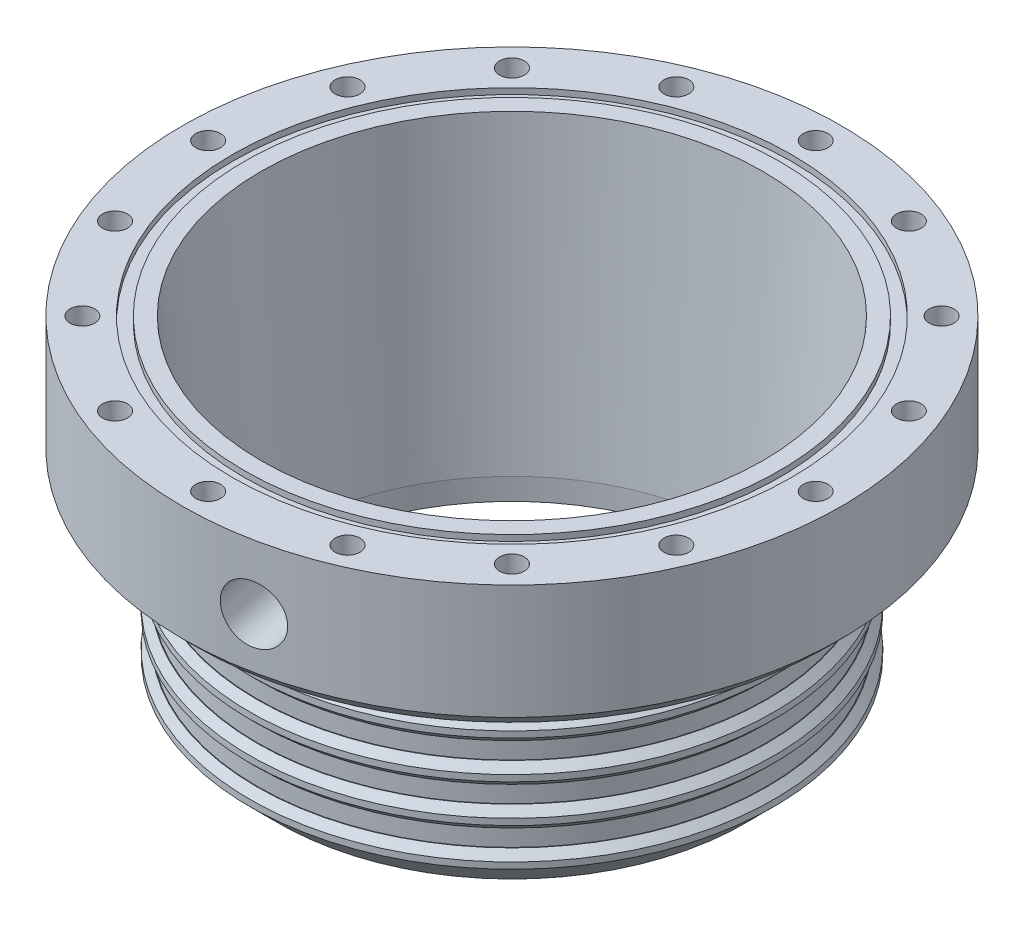
SolidWorks part; units mm, degrees
material "6061-T4 (SS)"
ref_plane "Front Plane" through (0, 0, 0) normal (0, 0, 1) x (1, 0, 0)
ref_plane "Top Plane" through (0, 0, 0) normal (0, 1, 0) x (1, 0, 0)
ref_plane "Right Plane" through (0, 0, 0) normal (1, 0, 0) x (0, 0, -1)
sketch "Sketch1" plane through (0, 0, 0) normal (0, 1, 0) x (1, 0, 0)
  circle A0 centre (0, 0) radius 55.5625
  circle A1 centre (0, 0) radius 58.1025
  dimension "D1" = 111.125
  dimension "D2" = 2.54
extrude "Boss-Extrude1" add sketch "Sketch1" along normal blind 38.1
sketch "Sketch2" plane through (0, 38.1, 0) normal (0, 1, 0) x (1, 0, 0)
  circle A0 centre (0, 0) radius 55.5625
  circle A1 centre (0, 0) radius 73.025
  circle A2 centre (0, 0) radius 55.5625 construction
  dimension "D1" = 146.05
extrude "Boss-Extrude2" add sketch "Sketch2" along normal blind 28.575
sketch "Sketch7" plane through (0, 0, 0) normal (0, 0, 1) x (1, 0, 0)
  line L0 (0, 0) -> (0, 88.9) construction
ref_plane "Plane1" through (0, 0, 0) normal (0.9659, 0, -0.2588) x (0, 1, 0)
ref_plane "Plane2" through (18.9003, 0, 70.5367) normal (0.2588, 0, 0.9659) x (0.9659, 0, -0.2588)
sketch "Sketch9" plane through (0, 0, 0) normal (0, 0, 1) x (1, 0, 0)
  line L0 (0, 0) -> (0, 88.9) construction
  line L2 (0, 0) -> (-58.1025, 0) construction
  line L3 (-58.1025, 0) -> (58.1025, 0) construction
  line L4 (-58.1025, 0) -> (-58.1025, 38.1) construction
  line L5 (-73.025, 38.1) -> (73.025, 38.1) construction
  line L6 (-58.1025, 38.1) -> (58.1025, 38.1) construction
  line L7 (-58.1025, 38.1) -> (-58.1025, 33.528)
  line L8 (-58.1025, 4.572) -> (-56.388, 4.572)
  line L9 (-58.1025, 4.572) -> (-58.1025, 8.382)
  line L10 (-58.1025, 8.382) -> (-56.388, 8.382)
  line L11 (-56.388, 4.572) -> (-56.388, 8.382)
  line L12 (-58.1025, 12.954) -> (-56.388, 12.954)
  line L13 (-58.1025, 12.954) -> (-58.1025, 16.764)
  line L14 (-58.1025, 16.764) -> (-56.388, 16.764)
  line L15 (-56.388, 12.954) -> (-56.388, 16.764)
  line L16 (-58.1025, 21.336) -> (-56.388, 21.336)
  line L17 (-58.1025, 21.336) -> (-58.1025, 25.146)
  line L18 (-58.1025, 25.146) -> (-56.388, 25.146)
  line L19 (-56.388, 21.336) -> (-56.388, 25.146)
  line L20 (-58.1025, 29.718) -> (-56.388, 29.718)
  line L21 (-58.1025, 29.718) -> (-58.1025, 33.528)
  line L22 (-58.1025, 33.528) -> (-56.388, 33.528)
  line L23 (-56.388, 29.718) -> (-56.388, 33.528)
  line L24 (-58.1025, 29.718) -> (-58.1025, 25.146)
  line L25 (-58.1025, 21.336) -> (-58.1025, 16.764)
  line L26 (-58.1025, 12.954) -> (-58.1025, 8.382)
  line L27 (-58.1025, 4.572) -> (-58.1025, 0)
  dimension "D1" = 58.1025
  dimension "D2" = 1.7145
  dimension "D3" = 3.81
revolve "Cut-Revolve1" cut sketch "Sketch9" angle 360 about L0
chamfer "Chamfer1" distance 1.5875 angle 45 1 edges at (0, 0, 58.1025)
sketch "Sketch10" plane through (0, 0, 0) normal (0, 0, 1) x (1, 0, 0)
  line L0 (0, 0) -> (0, 88.7441) construction
  line L1 (0, 0) -> (55.5625, 0) construction
  line L2 (55.5625, 0) -> (55.5625, 66.675)
  line L3 (55.5625, 66.675) -> (50.8, 0)
  line L4 (50.8, 0) -> (55.5625, 0)
  dimension "D1" = 55.5625
  dimension "D2" = 66.675
  dimension "D3" = 50.8
revolve "Revolve1" add sketch "Sketch10" angle 360 about L0
sketch "Sketch11" plane through (0, 66.675, 0) normal (0, 1, 0) x (1, 0, 0)
  circle A0 centre (0, 0) radius 61.9633
  circle A1 centre (0, 0) radius 59.3217
  dimension "D1" = 123.9266
  dimension "D2" = 2.6416
extrude "Cut-Extrude5" cut sketch "Sketch11" against normal blind 1.3208
sketch "Sketch12" plane through (0, 66.675, 0) normal (0, 1, 0) x (1, 0, 0)
  circle A0 centre (0, 0) radius 67.31 construction
  circle A1 centre (0, -67.31) radius 2.7432
  dimension "D1" = 5.4864
  dimension "D2" = 134.62
extrude "Cut-Extrude7" cut sketch "Sketch12" against normal blind 20.955 contours A1
pattern_circular "CirPattern2" count 16 over 360 about axis through (0, 0, 0) along (0, 1, 0) of "Cut-Extrude7"
sketch "Sketch13" plane through (0, 0, 0) normal (0, 0, 1) x (1, 0, 0)
  line L0 (0, 0) -> (50.8, 0) construction
  line L1 (0, 0) -> (0, 34.9502) construction
  line L2 (50.8, 0) -> (56.515, 0)
  line L3 (50.8, 0) -> (50.8, -5.715)
  line L4 (56.515, 0) -> (50.8, -5.715)
  dimension "D1" = 50.8
  dimension "D2" = 5.715
  dimension "D3" = 45
revolve "Revolve2" add sketch "Sketch13" angle 360 about L1
chamfer "Chamfer2" distance 1.27 angle 45 1 edges at (0, -5.715, -50.8)
sketch "Sketch14" plane through (0, 66.675, 0) normal (0, 1, 0) x (1, 0, 0)
  line L0 (0, -67.31) -> (25.7584, -62.1863) construction
  line L1 (0, -36.6713) -> (0, 36.6713) construction
  line L2 (0, 0) -> (12.8792, -64.7482) construction
  circle A1 centre (0, -67.31) radius 2.7432 construction
ref_plane "Plane3" through (12.8792, 0, 64.7482) normal (0.1951, 0, 0.9808) x (0.9808, 0, -0.1951)
sketch "Sketch15" plane through (12.8792, 0, 64.7482) normal (0.1951, 0, 0.9808) x (0.9808, 0, -0.1951)
  line L0 (0, 66.675) -> (0, 38.1) construction
  line L1 (-58.1025, 38.1) -> (58.1025, 38.1) construction
  circle A0 centre (0, 52.3875) radius 6.35
  dimension "D1" = 12.7
extrude "Cut-Extrude8" cut sketch "Sketch15" against normal up to next and the other way through all
chamfer "Chamfer3" distance 1.5875 angle 45 8 edges at (0, 33.528, -58.1025) (0, 29.718, -58.1025) (0, 21.336, -58.1025) (0, 25.146, -58.1025) (0, 12.954, -58.1025) (0, 16.764, -58.1025) (0, 8.382, -58.1025) (0, 4.572, -58.1025)
chamfer "Chamfer4" distance 3.175 angle 45 1 edges at (0, 38.1, 73.025)
